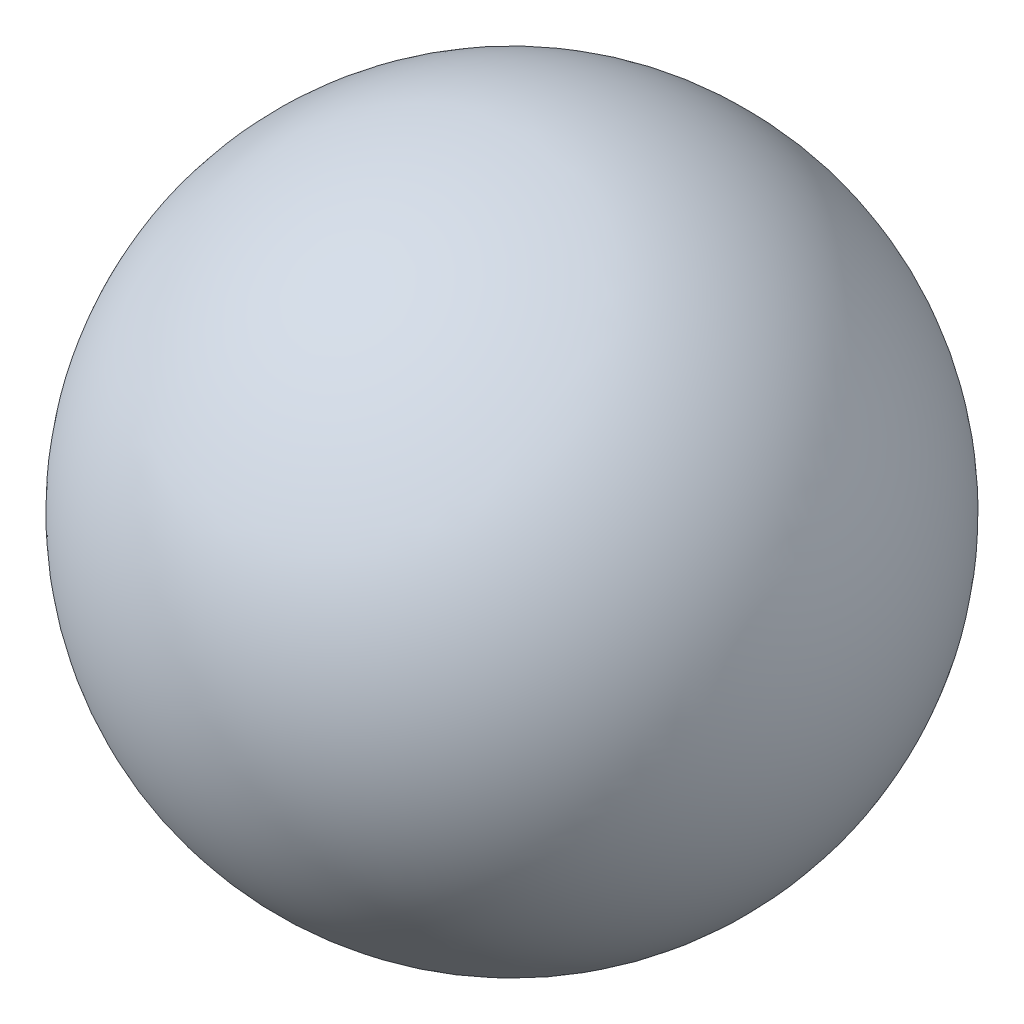
SolidWorks part; units mm, degrees
ref_plane "Front Plane" through (0, 0, 0) normal (0, 0, 1) x (1, 0, 0)
ref_plane "Top Plane" through (0, 0, 0) normal (0, 1, 0) x (1, 0, 0)
ref_plane "Right Plane" through (0, 0, 0) normal (1, 0, 0) x (0, 0, -1)
sketch "Sketch1" plane through (0, 0, 0) normal (0, 0, 1) x (1, 0, 0)
  line L0 (-12, 0) -> (12, 0)
  arc A0 (-12, 0) -> (12, 0) centre (0, 0) ccw
  point P4 (0, 0)
  point P5 (0, 0)
  dimension "D1" = 24
revolve "Revolve1" add sketch "Sketch1" angle 360 about L0
